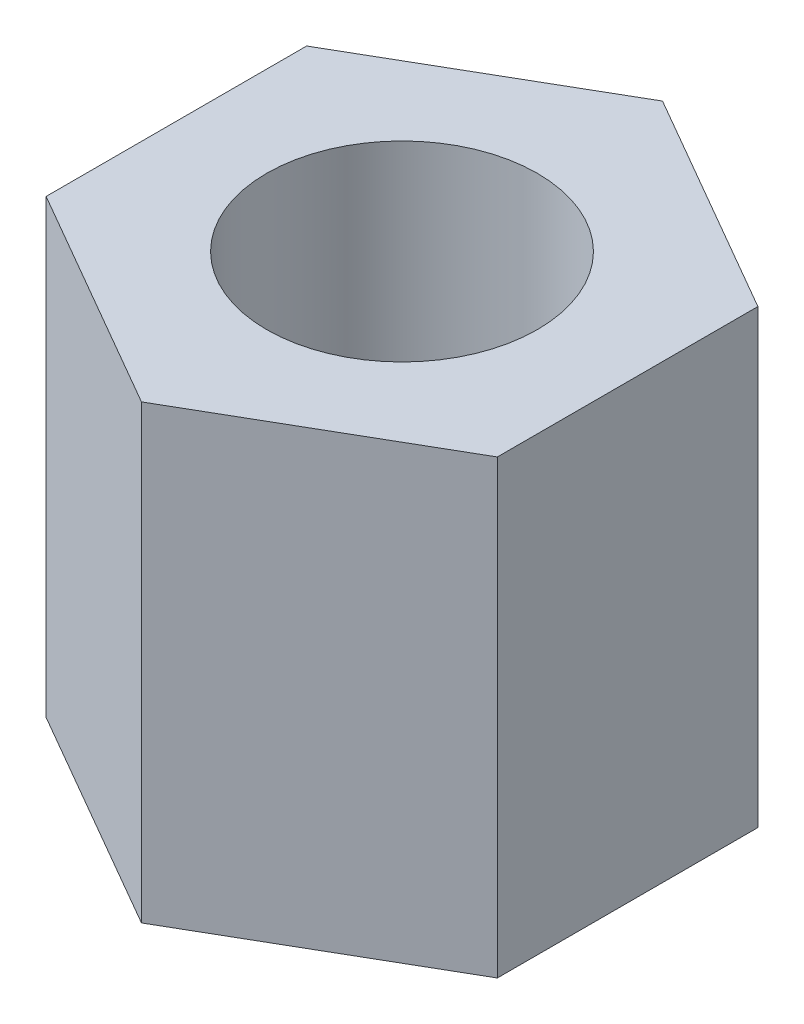
SolidWorks part; units mm, degrees
ref_plane "前基準面" through (0, 0, 0) normal (0, 0, 1) x (1, 0, 0)
ref_plane "上基準面" through (0, 0, 0) normal (0, 1, 0) x (1, 0, 0)
ref_plane "右基準面" through (0, 0, 0) normal (1, 0, 0) x (0, 0, -1)
sketch "草圖1" plane through (0, 0, 0) normal (0, 1, 0) x (1, 0, 0)
  line L0 (0, -5.1664) -> (0, 5.1664) construction
  line L1 (0, 2.8868) -> (-2.5, 1.4434)
  line L2 (-2.5, 1.4434) -> (-2.5, -1.4434)
  line L3 (-2.5, -1.4434) -> (0, -2.8868)
  line L4 (0, -2.8868) -> (2.5, -1.4434)
  line L5 (2.5, -1.4434) -> (2.5, 1.4434)
  line L6 (2.5, 1.4434) -> (0, 2.8868)
  circle A0 centre (0, 0) radius 1.5
  circle A1 centre (0, 0) radius 2.5 construction
  point P16 (0, 0)
  dimension "D1" = 3
  dimension "D2" = 5
extrude "填料-伸長1" add sketch "草圖1" along normal blind 5
